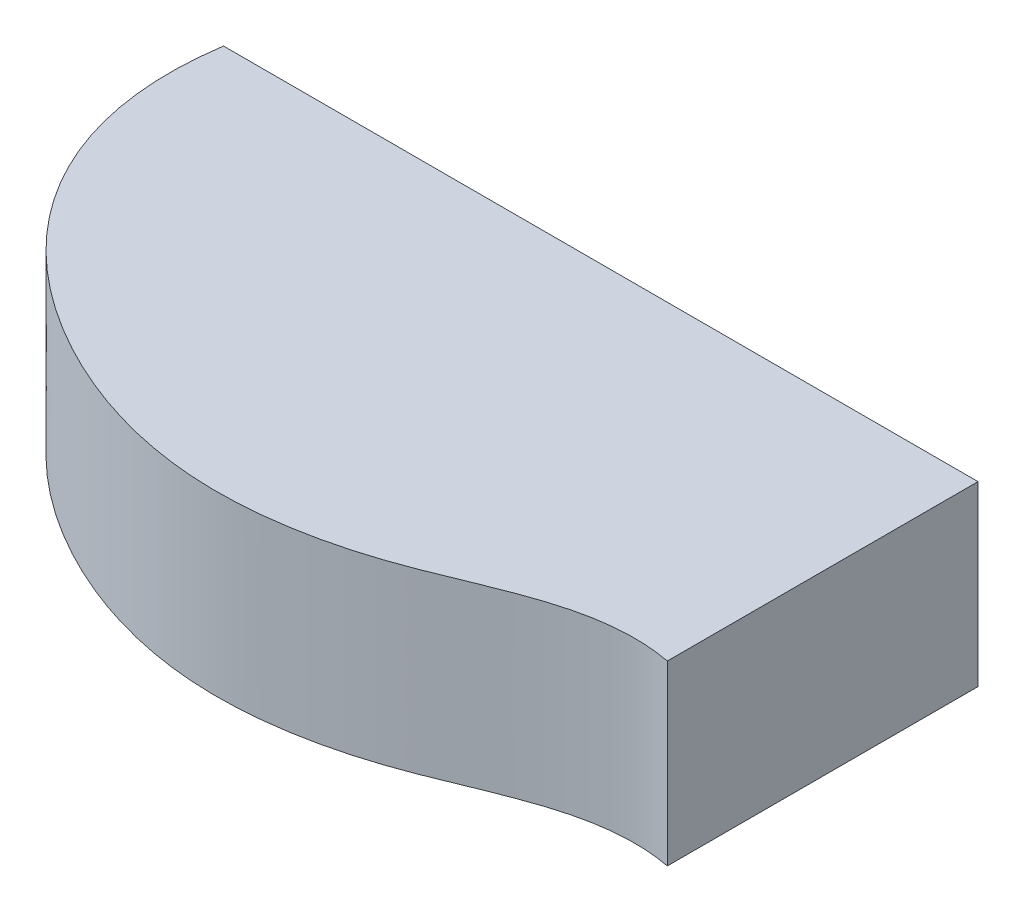
SolidWorks part; units mm, degrees
ref_plane "Front Plane" through (0, 0, 0) normal (0, 0, 1) x (1, 0, 0)
ref_plane "Top Plane" through (0, 0, 0) normal (0, 1, 0) x (1, 0, 0)
ref_plane "Right Plane" through (0, 0, 0) normal (1, 0, 0) x (0, 0, -1)
sketch "Sketch1" plane through (0, 0, 0) normal (0, 1, 0) x (1, 0, 0)
  line L0 (0, 0) -> (-107.95, 0)
  line L1 (0, 0) -> (0, -44.45)
  line L2 (-3.175, -3.175) -> (-105.1349, -3.175)
  line L3 (-3.175, -3.175) -> (-3.175, -40.8518)
  spline S0 degree 3 poles (-107.95, 0) (-111.2644, -22.2234) (-93.1283, -45.976) (-57.6096, -57.6978) (-28.7253, -52.8459) (-11.8195, -42.2097) (0, -44.45) knots 0 0 0 0 0.396764 0.585186 0.766935 1 1 1 1
  spline S1 degree 1 poles (-105.1349, -3.175) (-3.175, -40.8518) knots 0 0 1 1 construction
  spline S2 degree 3 poles (-105.1349, -3.175) (-105.2035, -3.9308) (-105.3034, -5.4613) (-105.343, -8.4077) (-105.1102, -11.9659) (-104.4079, -16.0165) (-102.946, -21.1455) (-100.1969, -27.0607) (-95.6095, -33.3908) (-89.9253, -38.9368) (-83.3536, -43.6609) (-76.1367, -47.5347) (-68.5133, -50.4217) (-60.6254, -52.2008) (-52.6399, -52.7294) (-44.5767, -52.031) (-37.9236, -50.544) (-32.7425, -48.8822) (-27.6075, -46.9043) (-22.3651, -44.6567) (-16.859, -42.6929) (-12.545, -41.5151) (-8.7559, -40.9183) (-5.6132, -40.7581) (-3.9812, -40.7992) (-3.175, -40.8518) knots 0.017398 0.017398 0.017398 0.017398 0.032398 0.047397 0.077396 0.107395 0.137393 0.197391 0.257389 0.317386 0.377384 0.437382 0.497379 0.557377 0.617375 0.677372 0.73737 0.767369 0.797368 0.857365 0.887364 0.917363 0.947362 0.962361 0.977361 0.977361 0.977361 0.977361
  dimension "D2" = 38.1
  dimension "D1" = 107.95
  dimension "D3" = 12.7
  dimension "D4" = 25.4
  dimension "D5" = 47.625
  dimension "D6" = 50.8
  dimension "D7" = 55.5625
  dimension "D8" = 76.2
  dimension "D9" = 51.8573
  dimension "D10" = 45.974
  dimension "D11" = 91.44
  dimension "D12" = 44.45
  dimension "D13" = 3.175
extrude "Boss-Extrude1" add sketch "Sketch1" along normal blind 3.175 contours S0 L1 L0
sketch "Sketch3" plane through (0, 3.175, 0) normal (0, 1, 0) x (1, 0, 0)
  line L0 (-107.95, 0) -> (0, 0)
  line L1 (0, 0) -> (0, -44.45)
  line L2 (-3.175, -3.175) -> (-3.175, -40.8518)
  line L3 (-105.1349, -3.175) -> (-3.175, -3.175)
  spline S0 degree 3 poles (-107.95, 0) (-111.2644, -22.2234) (-93.1283, -45.976) (-57.6096, -57.6978) (-28.7253, -52.8459) (-11.8195, -42.2097) (0, -44.45) knots 0 0 0 0 0.396764 0.585186 0.766935 1 1 1 1
  spline S1 degree 3 poles (-107.95, 0) (-111.2644, -22.2234) (-93.1283, -45.976) (-57.6096, -57.6978) (-28.7253, -52.8459) (-11.8195, -42.2097) (0, -44.45) knots 0 0 0 0 0.396764 0.585186 0.766935 1 1 1 1 construction
  spline S2 degree 1 poles (-105.1349, -3.175) (-3.175, -40.8518) knots 0 0 1 1 construction
  spline S3 degree 3 poles (-3.175, -40.8518) (-3.9812, -40.7992) (-5.6132, -40.7581) (-8.7559, -40.9183) (-12.545, -41.5151) (-16.859, -42.6929) (-22.3651, -44.6567) (-27.6075, -46.9043) (-32.7425, -48.8822) (-37.9236, -50.544) (-44.5767, -52.031) (-52.6399, -52.7294) (-60.6254, -52.2008) (-68.5133, -50.4217) (-76.1367, -47.5347) (-83.3536, -43.6609) (-89.9253, -38.9368) (-95.6095, -33.3908) (-100.1969, -27.0607) (-102.946, -21.1455) (-104.4079, -16.0165) (-105.1102, -11.9659) (-105.343, -8.4077) (-105.3034, -5.4613) (-105.2035, -3.9308) (-105.1349, -3.175) knots 0.017398 0.017398 0.017398 0.017398 0.032398 0.047397 0.077396 0.107395 0.137393 0.197391 0.22739 0.257389 0.317386 0.377384 0.437382 0.497379 0.557377 0.617375 0.677372 0.73737 0.797368 0.857365 0.887364 0.917363 0.947362 0.962361 0.977361 0.977361 0.977361 0.977361
  dimension "D1" = 12.7
  dimension "D2" = 25.4
  dimension "D3" = 50.8
  dimension "D4" = 91.44
  dimension "D5" = 76.2
  dimension "D6" = 3.175
extrude "Boss-Extrude2" add sketch "Sketch3" against normal blind 25.4 contours L1 S0 L0 | L2 S3 L3
sketch "Sketch4" plane through (0, -22.225, 0) normal (0, -1, 0) x (-1, 0, 0)
  circle A0 centre (105.1349, -3.175) radius 3.175
  circle A1 centre (3.175, -3.175) radius 3.175
  circle A2 centre (3.175, -40.8518) radius 3.175
  spline S0 degree 3 poles (3.175, -40.8518) (3.9812, -40.7992) (5.6132, -40.7581) (8.7559, -40.9183) (12.545, -41.5151) (16.859, -42.6929) (22.3651, -44.6567) (27.6075, -46.9043) (32.7425, -48.8822) (37.9236, -50.544) (44.5767, -52.031) (52.6399, -52.7294) (60.6254, -52.2008) (68.5133, -50.4217) (76.1367, -47.5347) (83.3536, -43.6609) (89.9253, -38.9368) (95.6095, -33.3908) (100.1969, -27.0607) (102.946, -21.1455) (104.4079, -16.0165) (105.1102, -11.9659) (105.343, -8.4077) (105.3034, -5.4613) (105.2035, -3.9308) (105.1349, -3.175) knots 0.017398 0.017398 0.017398 0.017398 0.032398 0.047397 0.077396 0.107395 0.137393 0.197391 0.22739 0.257389 0.317386 0.377384 0.437382 0.497379 0.557377 0.617375 0.677372 0.73737 0.797368 0.857365 0.887364 0.917363 0.947362 0.962361 0.977361 0.977361 0.977361 0.977361 construction
  dimension "D1" = 6.35
  dimension "D2" = 6.35
  dimension "D3" = 6.35
  dimension "D4" = 4.7987
extrude "Boss-Extrude3" add sketch "Sketch4" against normal blind 23.876
sketch "Sketch5" plane through (0, 0, 0) normal (0, -1, 0) x (1, 0, 0)
  line L1 (-6.35, 3.175) -> (-71.35, 3.175)
  line L2 (-6.35, 3.175) -> (-6.35, 38.675)
  line L3 (-6.35, 38.675) -> (-71.35, 38.675)
  line L4 (-71.35, 3.175) -> (-71.35, 38.675)
  dimension "D1" = 65
  dimension "D2" = 35.5
extrude "Boss-Extrude4" add sketch "Sketch5" along normal blind 21.14
